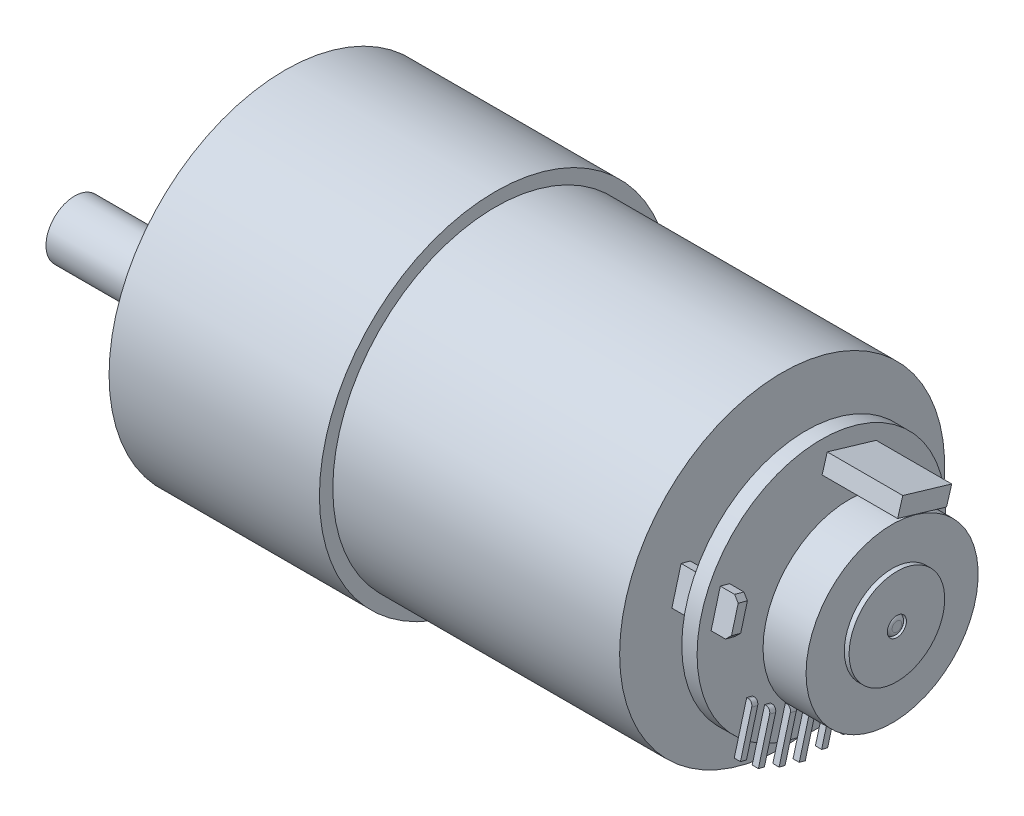
SolidWorks part; units mm, degrees
material "Pololu 37D"
ref_plane "Front Plane" through (0, 0, 0) normal (0, 0, 1) x (1, 0, 0)
ref_plane "Top Plane" through (0, 0, 0) normal (0, 1, 0) x (1, 0, 0)
ref_plane "Right Plane" through (0, 0, 0) normal (1, 0, 0) x (0, 0, -1)
sketch "Sketch1" plane through (0, 0, 0) normal (0, 0, 1) x (1, 0, 0)
  line L0 (0, 0) -> (64, 0)
  line L1 (52, 1) -> (54.5, 1)
  line L2 (54.5, 1) -> (54.5, 13)
  line L3 (52, 1) -> (52, 17)
  line L4 (52, 17) -> (22, 17)
  line L5 (22, 17) -> (22, 18.4)
  line L6 (22, 18.4) -> (0, 18.4)
  line L7 (0, 18.4) -> (0, 0)
  line L8 (54.5, 13) -> (56.1, 13)
  line L9 (56.1, 13) -> (56.1, 1)
  line L10 (56.1, 1) -> (59, 1)
  line L11 (59, 1) -> (59, 9)
  line L12 (59, 9) -> (63.5, 9)
  line L13 (63.5, 9) -> (63.5, 5)
  line L14 (63.5, 5) -> (64, 5)
  line L15 (64, 5) -> (64, 1)
  line L16 (64, 1) -> (63.5, 1)
  line L17 (64, 0.5) -> (64, 0)
  arc A0 (63.5, 1) -> (64, 0.5) centre (63.5, 0.5) cw
  dimension "D1" = 22
  dimension "D2" = 30
  dimension "D3" = 5
  dimension "D4" = 18.4
  dimension "D5" = 17
  dimension "D6" = 13
  dimension "D7" = 1
  dimension "D8" = 1.6
  dimension "D9" = 2.5
  dimension "D10" = 12
  dimension "D11" = 9
  dimension "D12" = 0.5
  dimension "D13" = 1
  dimension "D14" = 7
revolve "Revolve1" add sketch "Sketch1" angle 360 about L0
sketch "Sketch2" plane through (0, 0, 0) normal (-1, 0, 0) x (0, 0, 1)
  circle A0 centre (0, -7) radius 6
  dimension "D2" = 12
  dimension "D1" = 7
extrude "Boss-Extrude1" add sketch "Sketch2" along normal blind 6.5
sketch "Sketch3" plane through (-6.5, 0, 0) normal (-1, 0, 0) x (0, 0, 1)
  circle A0 centre (0, -7) radius 3
  dimension "D1" = 6
extrude "Boss-Extrude2" add sketch "Sketch3" along normal blind 15.5
sketch "Sketch4" plane through (-22, 0, 0) normal (-1, 0, 0) x (0, 0, 1)
  line L0 (1.5, -9.5981) -> (-1.5, -9.5981)
  circle A0 centre (0, -7) radius 3 construction
  arc A1 (-1.5, -9.5981) -> (1.5, -9.5981) centre (0, -7) ccw
  dimension "D1" = 3
extrude "Cut-Extrude1" cut sketch "Sketch4" against normal blind 12
chamfer "Chamfer1" distance 1 angle 45 1 edges at (-6.5, -7, 6)
sketch "Sketch5" plane through (0, 0, 0) normal (-1, 0, 0) x (0, 0, 1)
  circle A0 centre (15.5, 0) radius 1.23
  dimension "D1" = 2.46
  dimension "D2" = 15.5
extrude "Cut-Extrude2" cut sketch "Sketch5" against normal blind 5
pattern_circular "CirPattern1" count 6 over 360 about axis through (0, 0, 0) along (1, 0, 0) of "Cut-Extrude2"
sketch "Sketch6" plane through (56.1, 0, 0) normal (1, 0, 0) x (0, 0, -1)
  line L0 (0.6145, 11.5591) -> (5.7344, 10.0452)
  line L1 (0.6145, 11.5591) -> (0.0765, 9.7397)
  line L2 (5.7344, 10.0452) -> (5.1964, 8.2257)
  line L3 (0.0765, 9.7397) -> (5.1964, 8.2257)
extrude "Boss-Extrude3" add sketch "Sketch6" along normal up to surface (7.9 mm away) up to face at (64, 0, 5)
sketch "Sketch7" plane through (52, 0, 0) normal (1, 0, 0) x (0, 0, -1)
  line L0 (-10.5696, 4.9937) -> (-11.5324, 1.4314)
  line L1 (-10.5696, 4.9937) -> (-9.6043, 4.7328)
  line L2 (-11.5324, 1.4314) -> (-10.5671, 1.1705)
  line L3 (-9.6043, 4.7328) -> (-10.5671, 1.1705)
  line L4 (10.9602, -0.8251) -> (9.9974, -4.3875)
  line L5 (10.9602, -0.8251) -> (11.9256, -1.086)
  line L6 (9.9974, -4.3875) -> (10.9628, -4.6484)
  line L7 (11.9256, -1.086) -> (10.9628, -4.6484)
  dimension "D1" = 1
extrude "Boss-Extrude4" add sketch "Sketch7" along normal offset from surface (6.1 mm away) 2 up to face at (56.1, 0, 1) offset beyond the face yes
chamfer "Chamfer2" distance 0.5 angle 45 4 edges at (58.1, -4.518, -10.4801) (58.1, -0.9556, -11.4429) (58.1, 1.3009, 11.0498) (58.1, 4.8633, 10.087)
sketch "Sketch9" plane through (56.1, 0, 0) normal (1, 0, 0) x (0, 0, -1)
  line L0 (-7.8077, -6.481) -> (-9.1122, -11.3078)
  line L1 (-7.8077, -6.481) -> (-7.1802, -6.6506)
  line L2 (-9.1122, -11.3078) -> (-8.4848, -11.4774)
  line L3 (-7.1802, -6.6506) -> (-8.4848, -11.4774)
  line L4 (-10.5671, 1.1705) -> (-9.6043, 4.7328) construction
  line L5 (-5.9326, -8.0526) -> (-7.2372, -12.8794)
  line L6 (-5.9326, -8.0526) -> (-5.3051, -8.2222)
  line L7 (-7.2372, -12.8794) -> (-6.6097, -13.049)
  line L8 (-5.3051, -8.2222) -> (-6.6097, -13.049)
  line L9 (-3.7695, -8.9959) -> (-5.074, -13.8227)
  line L10 (-3.7695, -8.9959) -> (-3.142, -9.1655)
  line L11 (-5.074, -13.8227) -> (-4.4465, -13.9923)
  line L12 (-3.142, -9.1655) -> (-4.4465, -13.9923)
  line L13 (-1.6579, -9.6219) -> (-2.9624, -14.4487)
  line L14 (-1.6579, -9.6219) -> (-1.0304, -9.7915)
  line L15 (-2.9624, -14.4487) -> (-2.3349, -14.6183)
  line L16 (-1.0304, -9.7915) -> (-2.3349, -14.6183)
  line L17 (0.6801, -9.6246) -> (-0.6244, -14.4514)
  line L18 (0.6801, -9.6246) -> (1.3076, -9.7942)
  line L19 (-0.6244, -14.4514) -> (0.003, -14.621)
  line L20 (1.3076, -9.7942) -> (0.003, -14.621)
  line L21 (2.9201, -9.3953) -> (1.6156, -14.2221)
  line L22 (2.9201, -9.3953) -> (3.5476, -9.5648)
  line L23 (1.6156, -14.2221) -> (2.2431, -14.3917)
  line L24 (3.5476, -9.5648) -> (2.2431, -14.3917)
  dimension "D1" = 0.65
  dimension "D2" = 5
extrude "Boss-Extrude5" add sketch "Sketch9" along normal blind 0.65
fillet "Fillet1" radius 0.5 6 edges at (56.75, -9.48, -3.2339) (56.75, -9.7094, -0.9938) (56.75, -9.7067, 1.3441) (56.75, -9.0807, 3.4557) (56.75, -8.1374, 5.6189) (56.75, -6.5658, 7.494)
sketch "Sketch10" plane through (0, -12.8331, 3.4684) normal (0, -0.9654, 0.2609) x (1, 0, 0)
  line L0 (56.75, 5.1963) -> (56.1, 5.1963) construction
  line L1 (56.75, 5.8463) -> (56.1, 5.8463) construction
  line L3 (56.75, 5.8463) -> (56.75, 5.1963) construction
  line L4 (56.75, 3.6261) -> (56.75, 2.9761) construction
  line L5 (56.75, 2.9761) -> (56.1, 2.9761) construction
  line L6 (56.75, 3.6261) -> (56.1, 3.6261) construction
  circle A0 centre (56.425, 5.5213) radius 0.325
  circle A1 centre (56.425, 3.3011) radius 0.325
sketch "Sketch13" plane through (0, -12.847, 3.4722) normal (0, -0.9654, 0.2609) x (1, 0, 0)
  line L0 (56.75, -5.2703) -> (56.75, -5.9203) construction
  line L1 (56.75, -5.9203) -> (56.1, -5.9203) construction
  circle A0 centre (56.425, -5.5953) radius 0.325
  circle A1 centre (56.425, -3.4053) radius 0.325
  circle A2 centre (56.425, -1.2153) radius 0.325
  circle A3 centre (56.425, 0.9747) radius 0.325
  dimension "D1" = 0.65
  dimension "D2" = 4
sketch "Sketch14" plane through (0, 0, 0) normal (-1, 0, 0) x (0, 0, 1)
  arc A0 (-9.6139, -7.1815) -> (9.6139, -7.1815) centre (0, 0) cw
  arc A1 (-7.9936, -6.679) -> (7.9936, -6.679) centre (0, -7) cw
  arc A2 (-9.6139, -7.1815) -> (-7.9936, -6.679) centre (-8.8928, -6.6429) ccw
  arc A3 (7.9936, -6.679) -> (9.6139, -7.1815) centre (8.8928, -6.6429) ccw
  dimension "D1" = 12
  dimension "D2" = 8
  dimension "D3" = 0.9
extrude "Cut-Extrude3" cut sketch "Sketch14" against normal blind 1
